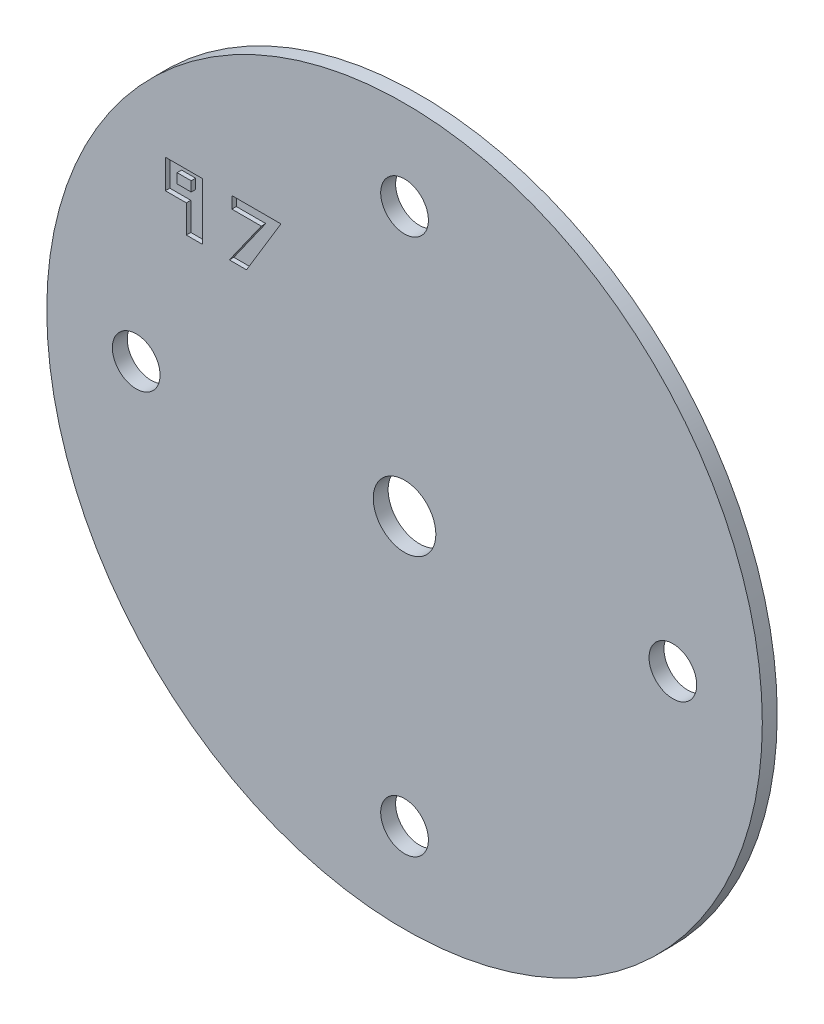
SolidWorks part; units mm, degrees
ref_plane "Front Plane" through (0, 0, 0) normal (0, 0, 1) x (1, 0, 0)
ref_plane "Top Plane" through (0, 0, 0) normal (0, 1, 0) x (1, 0, 0)
ref_plane "Right Plane" through (0, 0, 0) normal (1, 0, 0) x (0, 0, -1)
sketch "Sketch1" plane through (0, 0, 0) normal (0, 0, 1) x (1, 0, 0)
  circle A0 centre (0, 0) radius 24
extrude "Boss-Extrude1" add sketch "Sketch1" along normal blind 1
sketch "Sketch2" plane through (0, 0, 1) normal (0, 0, 1) x (1, 0, 0)
  circle A0 centre (-18, 0) radius 1.6
  circle A1 centre (0, 18) radius 1.6
  circle A2 centre (18, 0) radius 1.6
  circle A3 centre (0, -18) radius 1.6
  dimension "D1" = 18
sketch "Sketch3" plane through (0, 0, 1) normal (0, 0, 1) x (1, 0, 0)
  circle A1 centre (0, 0) radius 2.1
extrude "Cut-Extrude2" cut sketch "Sketch3" against normal blind 2
extrude "Cut-Extrude3" cut sketch "Sketch2" against normal through all
sketch "Sketch4" plane through (0, 0, 1) normal (0, 0, 1) x (1, 0, 0)
  line L0 (-11.5857, 12.8419) -> (-8.2915, 12.8419)
  line L1 (-8.2915, 12.8419) -> (-10.5972, 9.0199)
  line L2 (-10.5972, 9.0199) -> (-11.7519, 9.0199)
  line L3 (-11.7519, 9.0199) -> (-9.6077, 12.0526)
  line L4 (-9.6077, 12.0526) -> (-11.5857, 12.0526)
  line L5 (-11.5857, 12.0526) -> (-11.5857, 12.8419)
  line L6 (-13.5591, 12.8419) -> (-16.0447, 12.8419)
  line L7 (-16.0447, 12.8419) -> (-16.0447, 10.8894)
  line L8 (-16.0447, 10.8894) -> (-14.6392, 10.8894)
  line L9 (-14.6392, 10.8894) -> (-14.6392, 9.0199)
  line L10 (-14.6392, 9.0199) -> (-13.5591, 9.0199)
  line L11 (-13.5591, 9.0199) -> (-13.5591, 12.8419)
  line L12 (-15.255, 12.3361) -> (-14.3112, 12.3361)
  line L13 (-14.3112, 12.3361) -> (-14.3112, 11.6812)
  line L14 (-14.3112, 11.6812) -> (-15.255, 11.6812)
  line L15 (-15.255, 11.6812) -> (-15.255, 12.3361)
extrude "Cut-Extrude4" cut sketch "Sketch4" against normal blind 0.3
